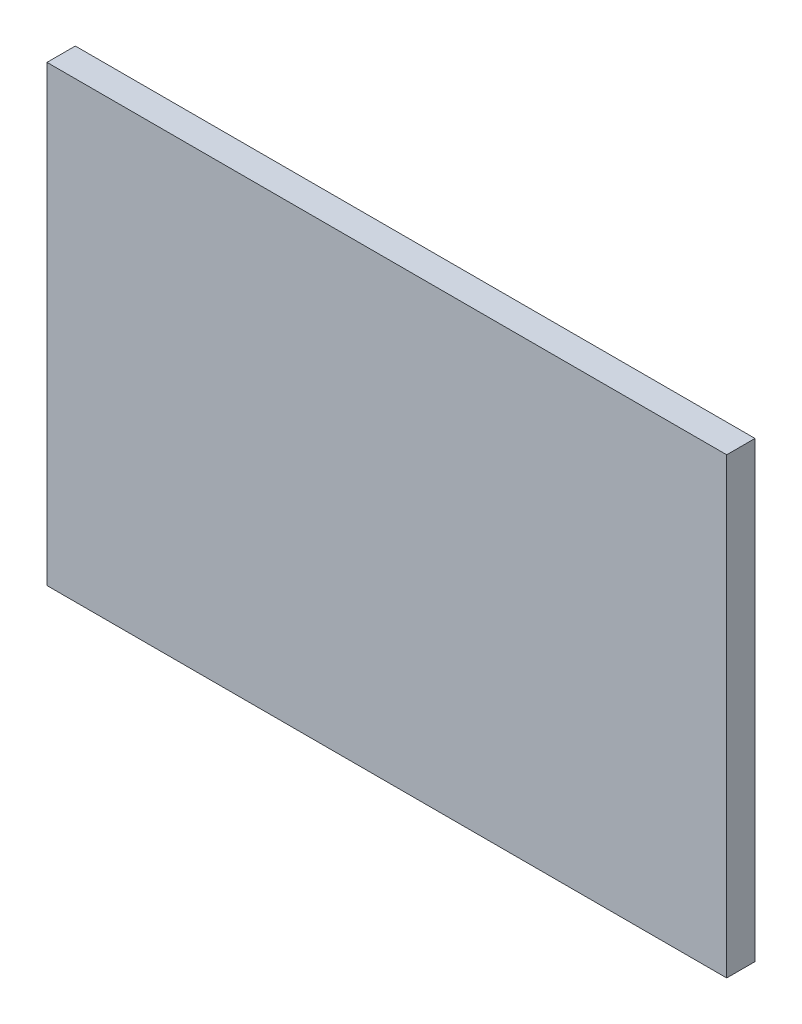
SolidWorks part; units mm, degrees
ref_plane "Front Plane" through (0, 0, 0) normal (0, 0, 1) x (1, 0, 0)
ref_plane "Top Plane" through (0, 0, 0) normal (0, 1, 0) x (1, 0, 0)
ref_plane "Right Plane" through (0, 0, 0) normal (1, 0, 0) x (0, 0, -1)
sketch "Sketch1" plane through (0, 0, 0) normal (0, 0, 1) x (1, 0, 0)
  line L1 (-76.2, -50.8) -> (76.2, -50.8)
  line L2 (-76.2, -50.8) -> (-76.2, 50.8)
  line L3 (-76.2, 50.8) -> (76.2, 50.8)
  line L4 (76.2, -50.8) -> (76.2, 50.8)
  line L5 (-76.2, -50.8) -> (76.2, 50.8) construction
  line L6 (-76.2, 50.8) -> (76.2, -50.8) construction
  point P0 (0, 0)
  dimension "D1" = 152.4
  dimension "D2" = 101.6
extrude "Boss-Extrude1" add sketch "Sketch1" along normal blind 6.35
